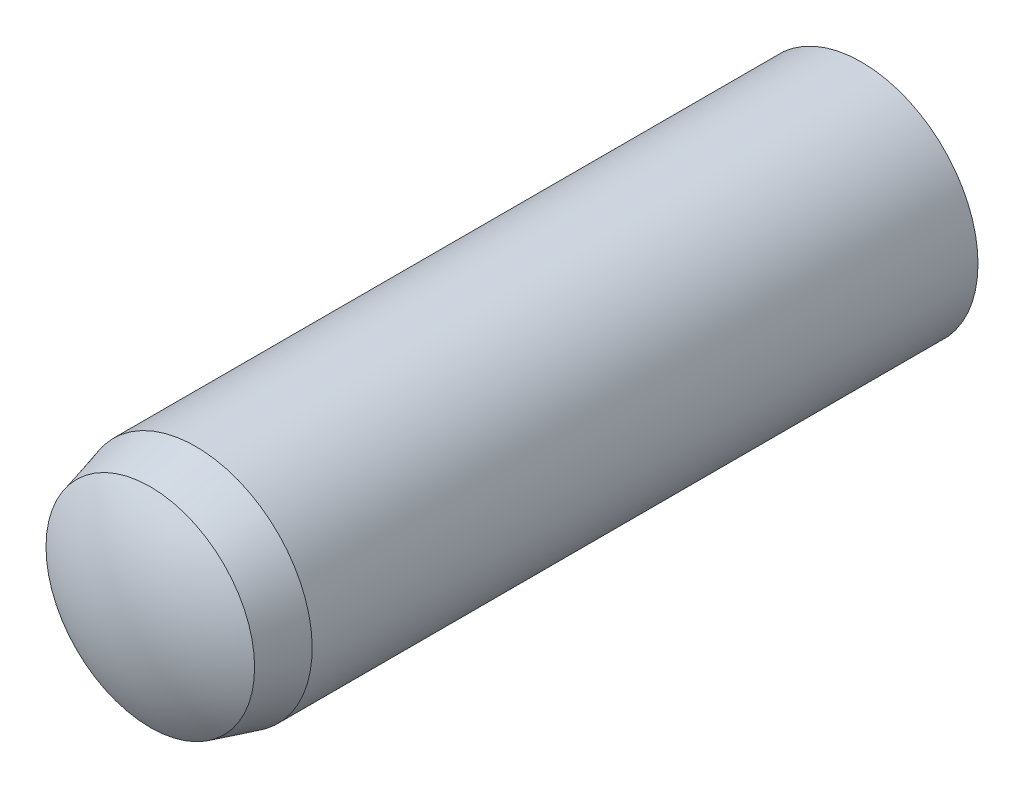
SolidWorks part; units mm, degrees
ref_plane "Front Plane" through (0, 0, 0) normal (0, 0, 1) x (1, 0, 0)
ref_plane "Top Plane" through (0, 0, 0) normal (0, 1, 0) x (1, 0, 0)
ref_plane "Right Plane" through (0, 0, 0) normal (1, 0, 0) x (0, 0, -1)
sketch "Sketch1" plane through (0, 0, 0) normal (0, 0, 1) x (1, 0, 0)
  circle A0 centre (0, 0) radius 3
  point P3 (0, 3)
  dimension "Diameter" = 6
sketch "Sketch2" plane through (0, 0, 0) normal (1, 0, 0) x (0, 0, -1)
  line L0 (-10, 0) -> (10, 0) construction
  line L1 (-10, 0) -> (-10, 3) construction
  line L2 (-10, 3) -> (10, 3)
  line L3 (10, 3) -> (10, 0) construction
  line L4 (-9.22, 2.6865) -> (-8.05, 3)
  arc A0 (-10, 0) -> (-9.22, 2.6865) centre (-4.9835, 0) cw
  arc A1 (10, 0) -> (9.1, 3) centre (4.55, 0) ccw
  point P2 (0, 0)
  point P11 (-4, 0)
  point P13 (4, 0)
  dimension "Length" = 20
  dimension "D1" = 15
  dimension "D2" = 0.9
  dimension "D3" = 1.95
  dimension "D4" = 1.17
  dimension "D5" = 6
  dimension "D6" = 6
sketch "Sketch3" plane through (0, 0, 0) normal (1, 0, 0) x (0, 0, -1)
  line L0 (-10, 0) -> (10, 0) construction
  line L1 (-9.22, 2.6865) -> (-8.05, 3) construction
  line L2 (-10, 0) -> (10, 0)
  line L3 (-9.22, 2.6865) -> (-8.05, 3)
  line L4 (-8.05, 3) -> (9.1, 3)
  arc A0 (10, 0) -> (9.1, 3) centre (4.55, 0) ccw construction
  arc A1 (-9.22, 2.6865) -> (-10, 0) centre (-4.9835, 0) ccw construction
  arc A2 (10, 0) -> (9.1, 3) centre (4.55, 0) ccw
  arc A3 (-9.22, 2.6865) -> (-10, 0) centre (-4.9835, 0) ccw
revolve "Revolve1" add sketch "Sketch3" angle 360 about L2
equation "\"D2@Sketch2\" = \"Diameter@Sketch1\" * .15"
equation "\"D3@Sketch2\" = \"Diameter@Sketch1\" * .325"
equation "\"D4@Sketch2\" = \"D3@Sketch2\" * .6"
equation "\"D5@Sketch2\"=\"Diameter@Sketch1\""
equation "\"D6@Sketch2\"=\"D5@sketch2\""
